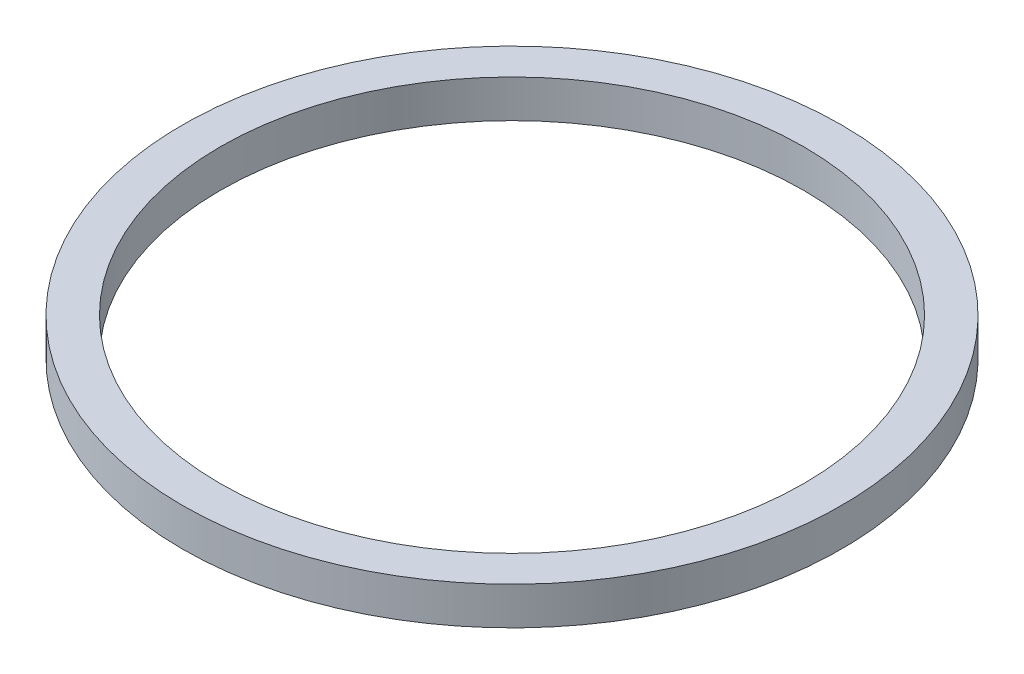
SolidWorks part; units mm, degrees
ref_plane "前视基准面" through (0, 0, 0) normal (0, 0, 1) x (1, 0, 0)
ref_plane "上视基准面" through (0, 0, 0) normal (0, 1, 0) x (1, 0, 0)
ref_plane "右视基准面" through (0, 0, 0) normal (1, 0, 0) x (0, 0, -1)
other "Configuration Table"
sketch "草图1" plane through (0, 0, 0) normal (0, 0, 1) x (1, 0, 0)
  line L0 (0, 0) -> (122, 0) construction
  line L1 (108, 7) -> (122, 7)
  line L2 (108, 7) -> (108, -7)
  line L3 (108, -7) -> (122, -7)
  line L4 (122, 7) -> (122, -7)
  line L5 (108, 0) -> (122, 0) construction
  line L6 (0, 0) -> (0, 31.8009) construction
  dimension "D1" = 14
  dimension "D2" = 108
  dimension "D3" = 14
revolve "旋转1" add sketch "草图1" angle 360 about L6
